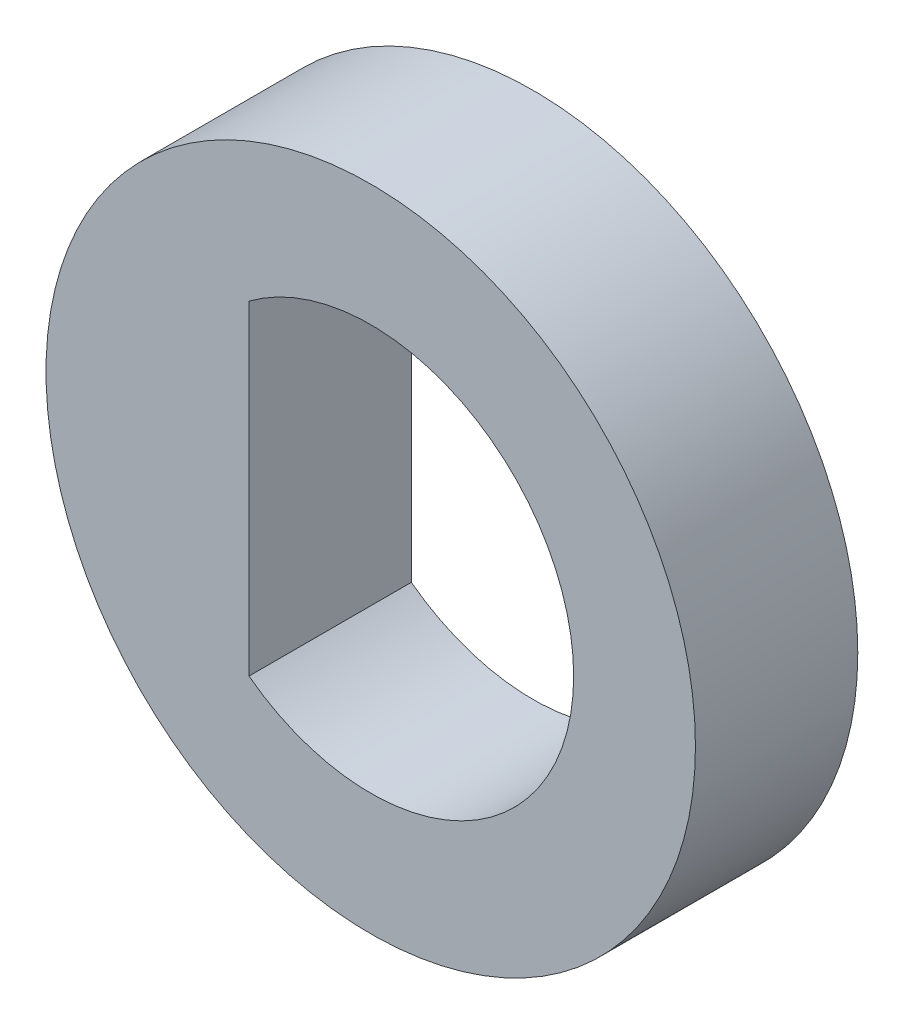
SolidWorks part; units mm, degrees
ref_plane "Front Plane" through (0, 0, 0) normal (0, 0, 1) x (1, 0, 0)
ref_plane "Top Plane" through (0, 0, 0) normal (0, 1, 0) x (1, 0, 0)
ref_plane "Right Plane" through (0, 0, 0) normal (1, 0, 0) x (0, 0, -1)
sketch "Sketch1" plane through (0, 0, 0) normal (0, 0, 1) x (1, 0, 0)
  line L4 (-1.5, 2) -> (-1.5, -2)
  arc A0 (-1.5, -2) -> (-1.5, 2) centre (0, 0) ccw
  circle A1 centre (0, 0) radius 4
  dimension "D1" = 5
  dimension "D2" = 8
  dimension "D4" = 1.5
extrude "Boss-Extrude1" add sketch "Sketch1" along normal blind 2
